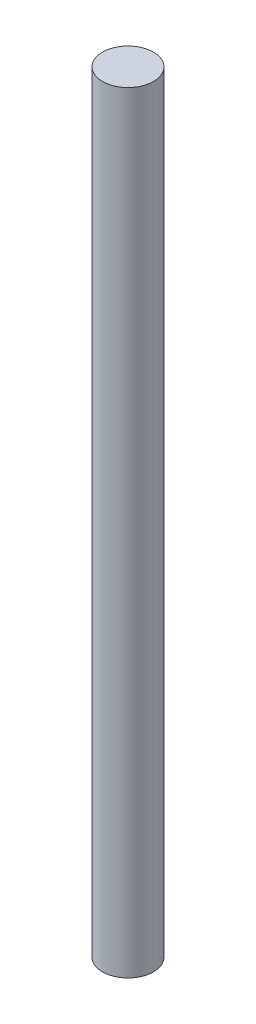
SolidWorks part; units mm, degrees
ref_plane "Front Plane" through (0, 0, 0) normal (0, 0, 1) x (1, 0, 0)
ref_plane "Top Plane" through (0, 0, 0) normal (0, 1, 0) x (1, 0, 0)
ref_plane "Right Plane" through (0, 0, 0) normal (1, 0, 0) x (0, 0, -1)
sketch "Sketch1" plane through (0, 0, 0) normal (0, 1, 0) x (1, 0, 0)
  circle A0 centre (0, 0) radius 2.5
  dimension "D1" = 5
extrude "Boss-Extrude1" add sketch "Sketch1" along normal blind 75.7
